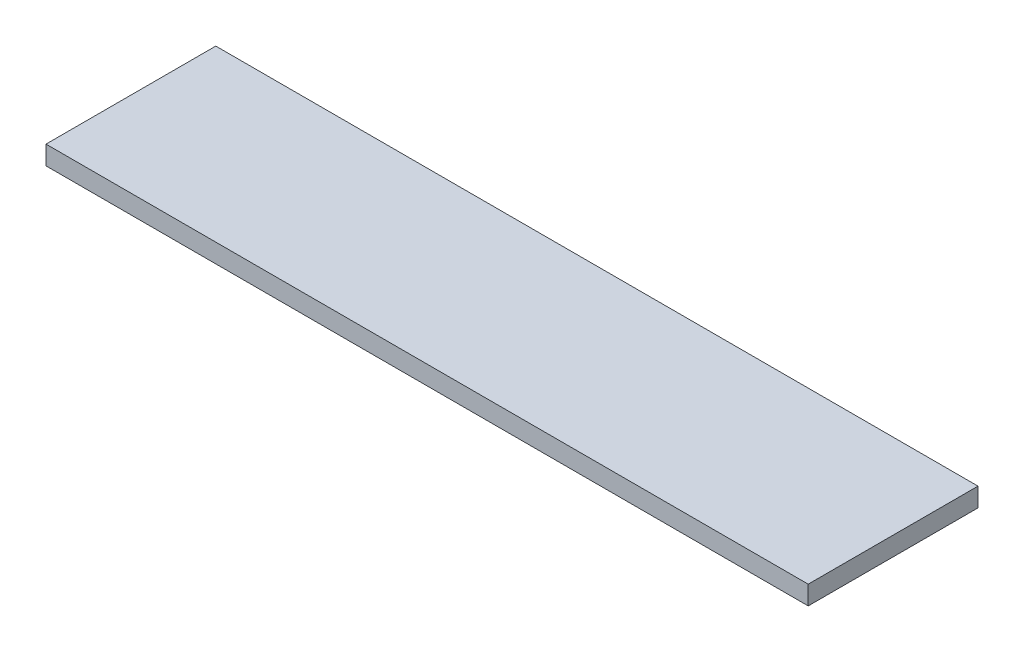
SolidWorks part; units mm, degrees
ref_plane "Plan de face" through (0, 0, 0) normal (0, 0, 1) x (1, 0, 0)
ref_plane "Plan de dessus" through (0, 0, 0) normal (0, 1, 0) x (1, 0, 0)
ref_plane "Plan de droite" through (0, 0, 0) normal (1, 0, 0) x (0, 0, -1)
sketch "Esquisse1" plane through (0, 0, 0) normal (0, 0, 1) x (1, 0, 0)
  line L1 (0, 0) -> (202, 0)
  line L2 (0, 0) -> (0, 5)
  line L3 (0, 5) -> (202, 5)
  line L4 (202, 0) -> (202, 5)
  dimension "D1" = 202
  dimension "D2" = 5
extrude "Boss.-Extru.1" add sketch "Esquisse1" along normal blind 45
